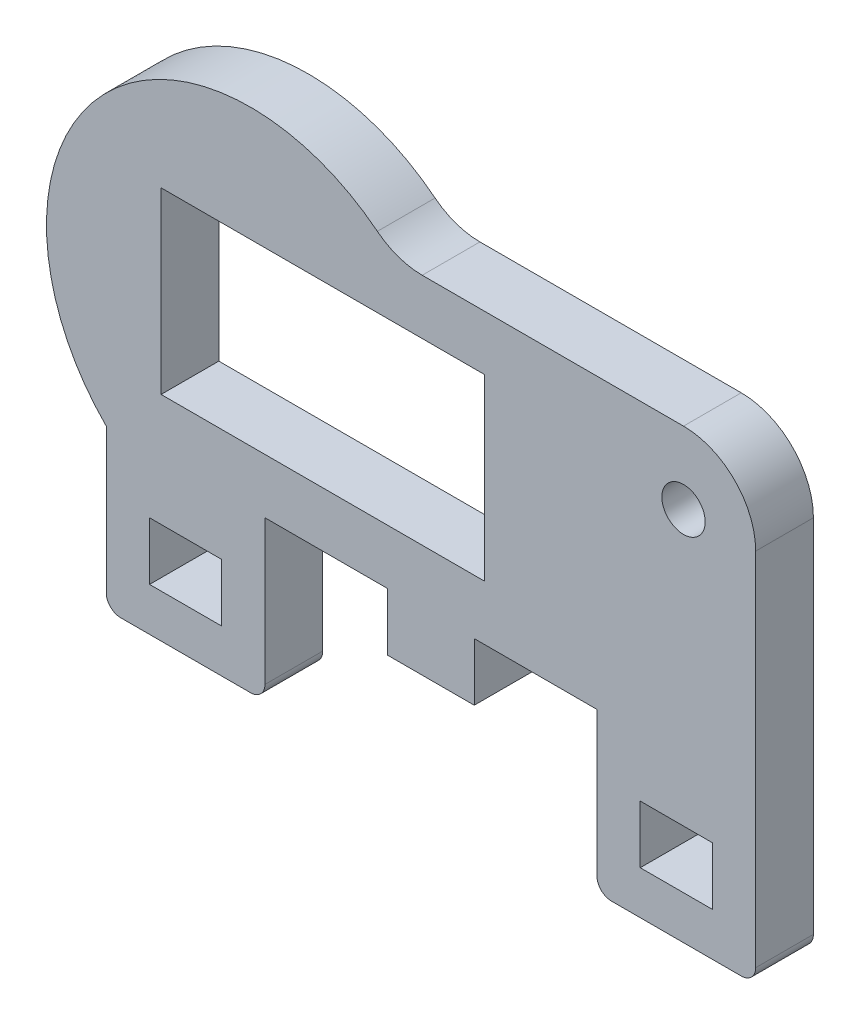
SolidWorks part; units mm, degrees
ref_plane "Front Plane" through (0, 0, 0) normal (0, 0, 1) x (1, 0, 0)
ref_plane "Top Plane" through (0, 0, 0) normal (0, 1, 0) x (1, 0, 0)
ref_plane "Right Plane" through (0, 0, 0) normal (1, 0, 0) x (0, 0, -1)
sketch "Sketch1" plane through (0, 0, 0) normal (0, 0, 1) x (1, 0, 0)
  line L5 (0, 0) -> (0, 20)
  line L7 (20, 20) -> (35, 20)
  line L8 (35, 20) -> (45, 20)
  line L9 (45, 20) -> (45, 0)
  line L10 (45, 0) -> (0, 0)
  line L11 (20, 20) -> (0, 20)
  line L12 (0, 0) -> (11, 0)
  line L13 (0, 0) -> (0, -11)
  line L14 (0, -11) -> (11, -11)
  line L15 (11, 0) -> (11, -11)
  line L16 (19.5, 0) -> (25.5, 0)
  line L17 (19.5, 0) -> (19.5, -4)
  line L18 (19.5, -4) -> (25.5, -4)
  line L19 (25.5, 0) -> (25.5, -4)
  line L20 (45, 0) -> (34, 0)
  line L21 (45, 0) -> (45, -11)
  line L22 (45, -11) -> (34, -11)
  line L23 (34, 0) -> (34, -11)
  line L24 (11, -4) -> (0, -4) construction
  line L25 (3.8, 16.2) -> (26.22, 16.2)
  line L26 (3.8, 16.2) -> (3.8, 3.8)
  line L27 (3.8, 3.8) -> (26.22, 3.8)
  line L28 (26.22, 16.2) -> (26.22, 3.8)
  line L29 (3, -8) -> (8, -8)
  line L30 (3, -8) -> (3, -4)
  line L31 (3, -4) -> (8, -4)
  line L32 (8, -8) -> (8, -4)
  line L33 (37, -8) -> (42, -8)
  line L34 (37, -8) -> (37, -4)
  line L35 (37, -4) -> (42, -4)
  line L36 (42, -8) -> (42, -4)
  line L37 (45, -4) -> (34, -4) construction
  circle A0 centre (10, 10) radius 0.8
  circle A1 centre (10, 10) radius 6.2
  arc A2 (15.4328, 7.0127) -> (15.4328, 12.9873) centre (15.7463, 10) ccw
  circle A3 centre (40, 15) radius 1.5
  circle A8 centre (10, 10) radius 14.1421
  point P8 (10, 10)
  point P16 (40, 20)
  point P18 (10, 20)
  point P20 (0, 10)
  point P22 (12.7425, 10)
  point P32 (22.5, -4)
  point P33 (22.5, 0)
  point P37 (3.8, 10)
  point P46 (39.5, -11)
  point P47 (39.5, -8)
  point P48 (5.5, -8)
  point P49 (5.5, -11)
  point P54 (5.5, -4)
  dimension "D3" = 1.6
  dimension "D4" = 12.4
  dimension "D6" = 5
  dimension "D1" = 3.0037
  dimension "D2" = 30
  dimension "D9" = 10
  dimension "D10" = 5
  dimension "D11" = 3
  dimension "D16" = 22.42
  dimension "D17" = 7
  dimension "D5" = 5.7463
  dimension "D7" = 10
  dimension "D8" = 45
  dimension "D12" = 4
  dimension "D13" = 11
  dimension "D14" = 4
  dimension "D15" = 6
  dimension "D18" = 4
  dimension "D19" = 5
  dimension "D20" = 5
  dimension "D21" = 4
extrude "Boss-Extrude2" add sketch "Sketch1" along normal blind 4 contours L5 A8 | L11 A8 | L25 A8 L11 L5 L10 L16 L27 L26 | A8 L13 L14 L15 L32 L29 L30 L31 | L10 A8 L15 | A8 L17 L18 L19 L10 | L17 A8 L16 | A8 L25 L28 L27 L10 L9 L8 L7 A3 | L10 L23 L22 L21 L36 L33 L34 L35
fillet "Fillet2" radius 1 4 edges at (45, -11, 2) (34, -11, 2) (0, -11, 2) (11, -11, 2)
fillet "Fillet1" radius 5 2 edges at (45, 20, 2) (20, 20, 2)
